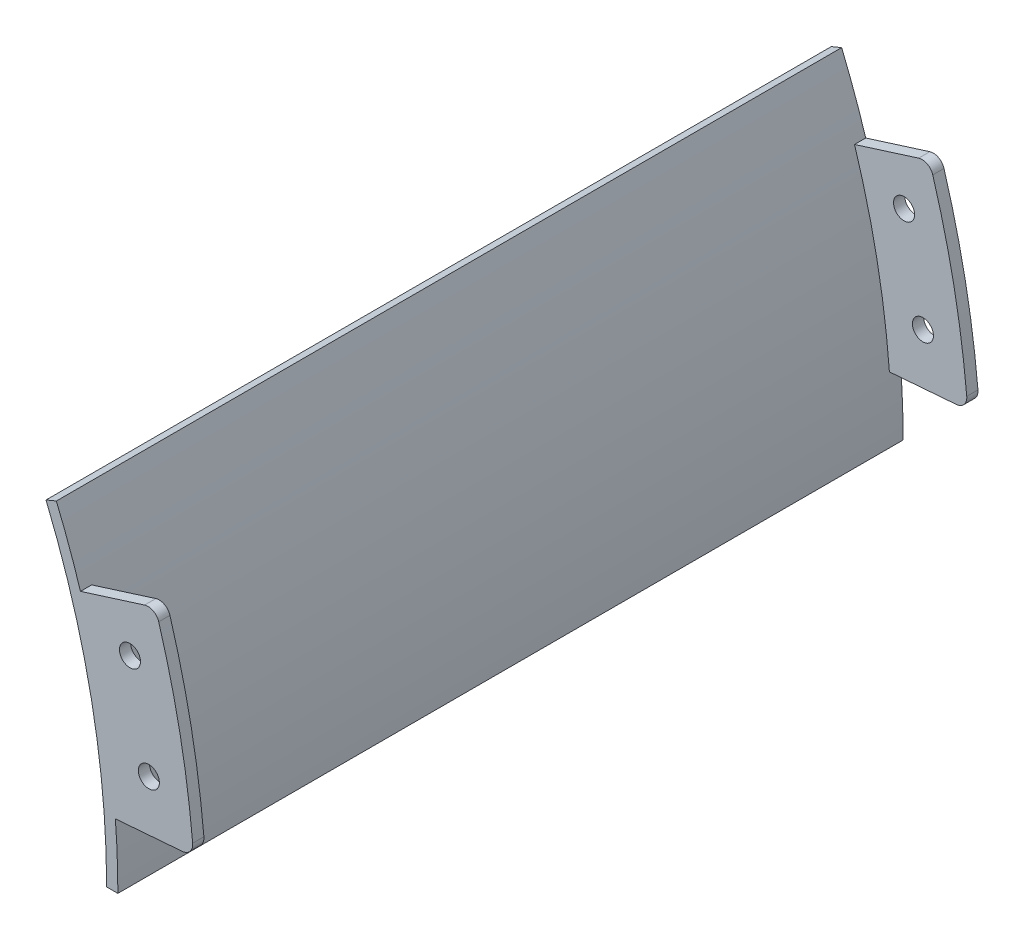
SolidWorks part; units mm, degrees
ref_plane "Front Plane" through (0, 0, 0) normal (0, 0, 1) x (1, 0, 0)
ref_plane "Top Plane" through (0, 0, 0) normal (0, 1, 0) x (1, 0, 0)
ref_plane "Right Plane" through (0, 0, 0) normal (1, 0, 0) x (0, 0, -1)
sketch "Sketch1" plane through (0, 0, 0) normal (0, 0, 1) x (1, 0, 0)
  line L0 (166.6124, 69.0131) -> (0, 0) construction
  line L1 (0, 0) -> (180.34, 0) construction
  line L2 (166.6124, 69.0131) -> (168.9591, 69.9851)
  line L3 (182.88, 0) -> (180.34, 0)
  arc A0 (166.6124, 69.0131) -> (180.34, 0) centre (0, 0) cw
  arc A1 (168.9591, 69.9851) -> (182.88, 0) centre (0, 0) cw
  dimension "D2" = 182.88
  dimension "D3" = 180.34
  dimension "D1" = 22.5
extrude "Boss-Extrude1" add sketch "Sketch1" along normal blind 177.8
sketch "Sketch2" plane through (0, 0, 177.8) normal (0, 0, 1) x (1, 0, 0)
  line L0 (174.4158, 54.9931) -> (188.9349, 59.5709)
  line L1 (197.493, 15.543) -> (182.3162, 14.3486)
  line L2 (0, 0) -> (200.0414, 15.7436) construction
  line L3 (0, 0) -> (191.3728, 60.3396) construction
  line L4 (168.9591, 69.9851) -> (166.6124, 69.0131) construction
  arc A0 (182.88, 0) -> (168.9591, 69.9851) centre (0, 0) ccw construction
  arc A1 (192.1307, 57.8812) -> (199.8232, 18.3069) centre (0, 0) cw
  arc A2 (180.34, 0) -> (166.6124, 69.0131) centre (0, 0) ccw construction
  arc A3 (174.4158, 54.9931) -> (182.3162, 14.3486) centre (0, 0) cw
  arc A4 (199.8232, 18.3069) -> (197.493, 15.543) centre (197.2937, 18.0752) cw
  arc A5 (188.9349, 59.5709) -> (192.1307, 57.8812) centre (189.6987, 57.1485) cw
  circle A6 centre (185.6265, 48.0012) radius 2.3813
  circle A7 centre (189.9046, 26.4112) radius 2.3813
  arc A8 (189.9046, 26.4112) -> (185.6265, 48.0012) centre (0, 0) ccw construction
  point P24 (189.9046, 14.9458)
  dimension "D1" = 2.54
  dimension "D4" = 17.78
  dimension "D5" = 4.7625
  dimension "D6" = 11.43
  dimension "D2" = 13
  dimension "D3" = 5
  dimension "D7" = 21.59
extrude "Boss-Extrude2" add sketch "Sketch2" against normal blind 2.54
ref_plane "Plane1" through (0, 0, 88.9) normal (0, 0, 1) x (1, 0, 0)
mirror "Mirror1" about plane through (0, 0, 88.9) normal (0, 0, 1) of "Boss-Extrude2"
